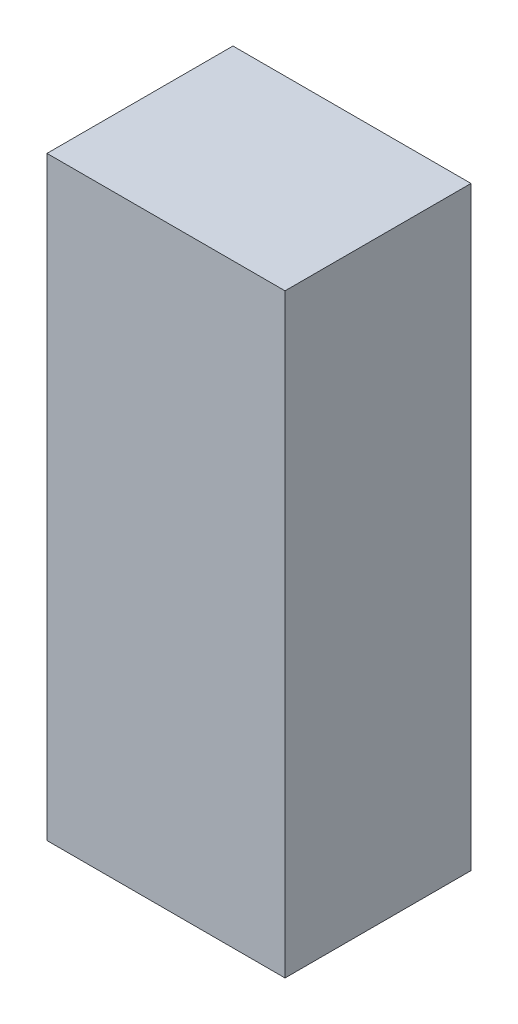
SolidWorks part; units mm, degrees
ref_plane "Front Plane" through (0, 0, 0) normal (0, 0, 1) x (1, 0, 0)
ref_plane "Top Plane" through (0, 0, 0) normal (0, 1, 0) x (1, 0, 0)
ref_plane "Right Plane" through (0, 0, 0) normal (1, 0, 0) x (0, 0, -1)
sketch "Sketch1" plane through (0, 0, 0) normal (0, 0, 1) x (1, 0, 0)
  line L0 (-48.4291, 0) -> (82.2989, 0) construction
  line L1 (-16, 40) -> (16, 40)
  line L2 (-16, 40) -> (-16, -40)
  line L3 (-16, -40) -> (16, -40)
  line L4 (16, 40) -> (16, -40)
  line L5 (0, 80.1533) -> (0, -79.0805) construction
  dimension "D1" = 80
  dimension "D2" = 32
extrude "Boss-Extrude1" add sketch "Sketch1" along normal blind 25
